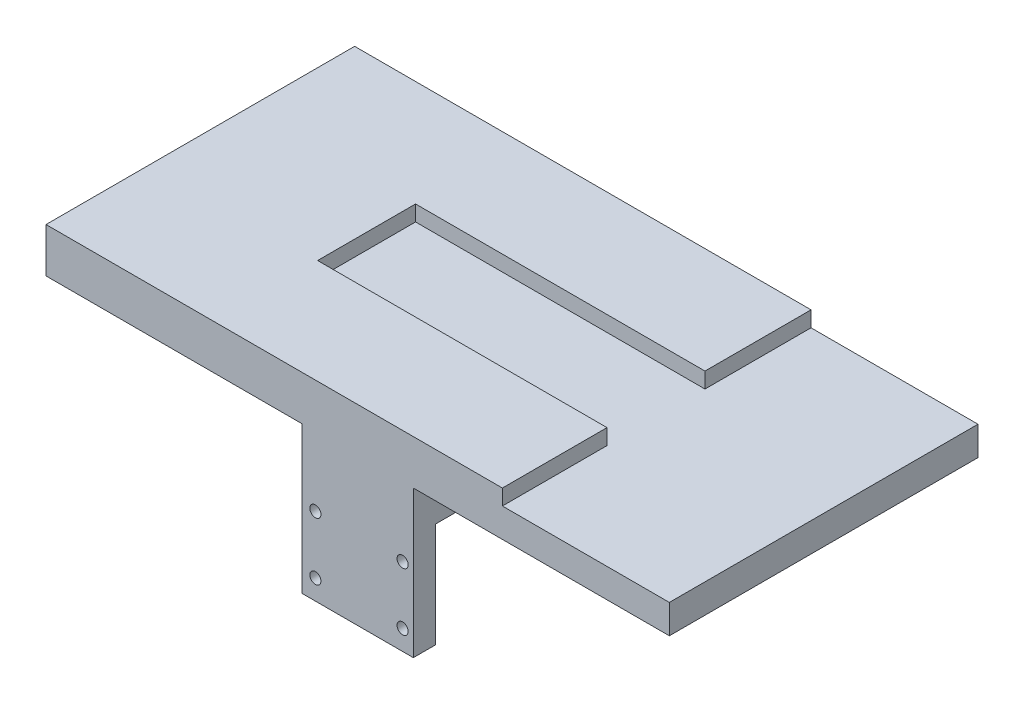
SolidWorks part; units mm, degrees
ref_plane "Front Plane" through (0, 0, 0) normal (0, 0, 1) x (1, 0, 0)
ref_plane "Top Plane" through (0, 0, 0) normal (0, 1, 0) x (1, 0, 0)
ref_plane "Right Plane" through (0, 0, 0) normal (1, 0, 0) x (0, 0, -1)
sketch "Sketch1" plane through (0, 0, 0) normal (0, 1, 0) x (1, 0, 0)
  line L1 (0, 0) -> (25, 0)
  line L2 (0, 0) -> (0, 38)
  line L3 (0, 38) -> (25, 38)
  line L4 (25, 0) -> (25, 38)
  dimension "D1" = 38
  dimension "D2" = 25
extrude "Boss-Extrude1" add sketch "Sketch1" along normal blind 12
ref_plane "Plane1" through (0, 0, -19) normal (0, 0, 1) x (1, 0, 0)
sketch "Sketch3" plane through (0, 0, 0) normal (0, 0, 1) x (1, 0, 0)
  line L1 (0, 12) -> (25, 12)
  line L2 (0, 12) -> (0, 0)
  line L3 (0, 0) -> (25, 0)
  line L4 (25, 12) -> (25, 0)
extrude "Boss-Extrude2" add sketch "Sketch3" along normal blind 5.5
sketch "Sketch5" plane through (0, 0, 0) normal (0, -1, 0) x (1, 0, 0)
  line L0 (25, 5.5) -> (25, -38) construction
  line L1 (0, 5.5) -> (25, 5.5)
  line L2 (0, 5.5) -> (0, 0.5)
  line L3 (0, 0.5) -> (25, 0.5)
  line L4 (25, 5.5) -> (25, 0.5)
  dimension "D1" = 5
extrude "Boss-Extrude3" add sketch "Sketch5" along normal blind 21
sketch "Sketch6" plane through (0, 0, 5.5) normal (0, 0, 1) x (1, 0, 0)
  line L0 (0, 12) -> (0, -21) construction
  line L2 (25, -21) -> (0, -21) construction
  circle A0 centre (3, -16.5) radius 1.25
  circle A1 centre (22.59, -16.5) radius 1.25
  circle A2 centre (22.59, -3.53) radius 1.25
  circle A3 centre (3, -3.53) radius 1.25
  dimension "D2" = 2.5
  dimension "D3" = 2.5
  dimension "D4" = 2.5
  dimension "D5" = 2.5
  dimension "D1" = 3
  dimension "D6" = 19.59
  dimension "D8" = 4.5
  dimension "D9" = 12.97
  dimension "D12" = 3
extrude "Cut-Extrude1" cut sketch "Sketch6" against normal blind 10
mirror "Mirror1" about plane through (0, 0, -19) normal (0, 0, 1) of "Cut-Extrude1", "Boss-Extrude3", "Boss-Extrude2"
sketch "Sketch7" plane through (0, 12, 0) normal (0, 1, 0) x (1, 0, 0)
  line L0 (12.5, 43.5) -> (12.5, -5.5) construction
  line L1 (25, 43.5) -> (0, 43.5) construction
  line L2 (25, -5.5) -> (0, -5.5) construction
  line L3 (0, 19) -> (25.0456, 19) construction
  line L4 (0, 43.5) -> (0, -5.5) construction
  line L5 (-6.6, 19) -> (6.6, 19) construction
  line L7 (-25, -5.5) -> (50, -5.5)
  line L8 (-25, -5.5) -> (-25, 43.5)
  line L9 (-25, 43.5) -> (50, 43.5)
  line L10 (50, -5.5) -> (50, 43.5)
  line L11 (-25, -5.5) -> (50, 43.5) construction
  line L12 (-25, 43.5) -> (50, -5.5) construction
  point P12 (12.5, 19)
  dimension "D1" = 75
  dimension "D2" = 49
extrude "Boss-Extrude4" add sketch "Sketch7" along normal blind 10
sketch "Sketch8" plane through (0, 22, 0) normal (0, 1, 0) x (1, 0, 0)
  line L0 (12.5, 43.5) -> (12.5, -5.5) construction
  line L1 (50, 43.5) -> (-25, 43.5) construction
  line L2 (-25, -5.5) -> (50, -5.5) construction
  line L3 (-25, 19) -> (50, 19) construction
  line L4 (-25, 43.5) -> (-25, -5.5) construction
  line L5 (50, -5.5) -> (50, 43.5) construction
  line L7 (-20, 23) -> (45, 23)
  line L8 (-20, 23) -> (-20, 35)
  line L9 (-20, 35) -> (45, 35)
  line L10 (45, 23) -> (45, 35)
  line L11 (-20, 23) -> (45, 35) construction
  line L12 (-20, 35) -> (45, 23) construction
  point P12 (12.5, 29)
  dimension "D1" = 10
  dimension "D2" = 12
  dimension "D3" = 65
extrude "Cut-Extrude2" cut sketch "Sketch8" against normal blind 3.5
sketch "Sketch11" plane through (0, 0, 0) normal (0, -1, 0) x (1, 0, 0)
  line L3 (0, -38.5) -> (25, -38.5)
  line L7 (0, -38.5) -> (0, 0.5)
  line L8 (0, 0.5) -> (25, 0.5)
  line L9 (25, 0.5) -> (25, -38.5)
extrude "Cut-Extrude4" cut sketch "Sketch11" against normal blind 2.5
sketch "Sketch12" plane through (0, 0, -43.5) normal (0, 0, -1) x (-1, 0, 0)
  line L1 (-50, 22) -> (25, 22)
  line L2 (-50, 22) -> (-50, 12)
  line L3 (-50, 12) -> (25, 12)
  line L4 (25, 22) -> (25, 12)
extrude "Boss-Extrude6" add sketch "Sketch12" along normal blind 20.32
ref_plane "Plane2" through (12.5, 0, 0) normal (1, 0, 0) x (0, 0, -1)
sketch "Sketch15" plane through (50, 0, 0) normal (1, 0, 0) x (0, 0, -1)
  line L1 (-5.5, 22) -> (63.82, 22)
  line L2 (-5.5, 22) -> (-5.5, 12)
  line L3 (-5.5, 12) -> (63.82, 12)
  line L4 (63.82, 22) -> (63.82, 12)
extrude "Boss-Extrude7" add sketch "Sketch15" along normal blind 32.5
sketch "Sketch16" plane through (-25, 0, 0) normal (-1, 0, 0) x (0, 0, 1)
  line L1 (-63.82, 22) -> (5.5, 22)
  line L2 (-63.82, 22) -> (-63.82, 12)
  line L3 (-63.82, 12) -> (5.5, 12)
  line L4 (5.5, 22) -> (5.5, 12)
extrude "Boss-Extrude8" add sketch "Sketch16" along normal blind 32.5
sketch "Sketch19" plane through (45, 0, 0) normal (-1, 0, 0) x (0, 0, 1)
  line L1 (-35, 22) -> (-23, 22)
  line L2 (-35, 22) -> (-35, 18.5)
  line L3 (-35, 18.5) -> (-23, 18.5)
  line L4 (-23, 22) -> (-23, 18.5)
extrude "Cut-Extrude6" cut sketch "Sketch19" against normal through all
sketch "Sketch23" plane through (0, 0, -35) normal (0, 0, 1) x (1, 0, 0)
  line L1 (-20, 22) -> (82.5, 22)
  line L2 (-20, 22) -> (-20, 18.5)
  line L3 (-20, 18.5) -> (82.5, 18.5)
  line L4 (82.5, 22) -> (82.5, 18.5)
extrude "Cut-Extrude7" cut sketch "Sketch23" against normal blind 5
sketch "Sketch24" plane through (0, 0, -23) normal (0, 0, -1) x (-1, 0, 0)
  line L1 (-82.5, 22) -> (20, 22)
  line L2 (-82.5, 22) -> (-82.5, 18.5)
  line L3 (-82.5, 18.5) -> (20, 18.5)
  line L4 (20, 22) -> (20, 18.5)
extrude "Cut-Extrude8" cut sketch "Sketch24" against normal blind 5
sketch "Sketch25" plane through (0, 22, 0) normal (0, 1, 0) x (1, 0, 0)
  line L0 (-57.5, -5.5) -> (82.5, -5.5) construction
  line L1 (82.5, 63.82) -> (45, 63.82)
  line L2 (82.5, 63.82) -> (82.5, -5.5)
  line L3 (82.5, -5.5) -> (45, -5.5)
  line L4 (45, 63.82) -> (45, -5.5)
  dimension "D1" = 37.5
extrude "Cut-Extrude9" cut sketch "Sketch25" against normal up to surface (3.5 mm away) up to face at (31.25, 18.5, -29)
